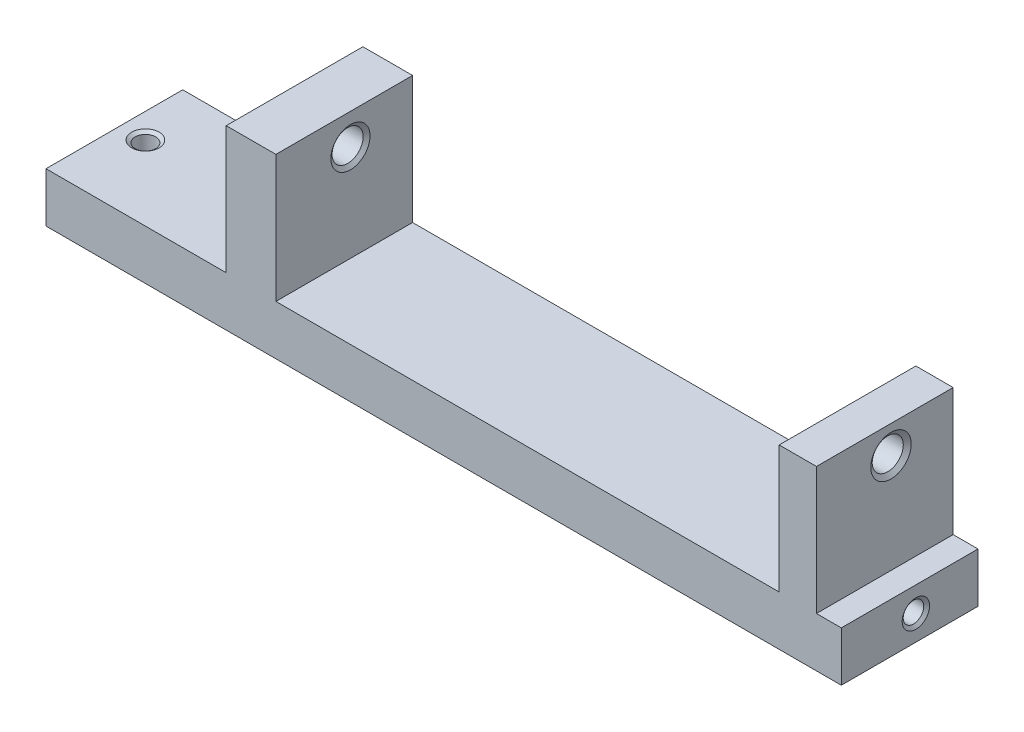
SolidWorks part; units mm, degrees
ref_plane "Спереди" through (0, 0, 0) normal (0, 0, 1) x (1, 0, 0)
ref_plane "Сверху" through (0, 0, 0) normal (0, 1, 0) x (1, 0, 0)
ref_plane "Справа" through (0, 0, 0) normal (1, 0, 0) x (0, 0, -1)
sketch "Эскиз1" plane through (0, 0, 0) normal (0, 0, 1) x (1, 0, 0)
  line L0 (0, 0) -> (128, 0)
  line L1 (128, 0) -> (128, 8)
  line L2 (124, 28.5) -> (118, 28.5)
  line L3 (118, 28.5) -> (118, 8)
  line L4 (118, 8) -> (37, 8)
  line L5 (37, 8) -> (37, 28.5)
  line L6 (37, 28.5) -> (29, 28.5)
  line L7 (29, 28.5) -> (29, 8)
  line L8 (29, 8) -> (0, 8)
  line L9 (0, 8) -> (0, 0)
  line L10 (128, 8) -> (124, 8)
  line L11 (124, 8) -> (124, 28.5)
  dimension "D1" = 128
  dimension "D2" = 8
  dimension "D3" = 6
  dimension "D4" = 8
  dimension "D5" = 81
  dimension "D6" = 4
  dimension "D7" = 28.5
extrude "Бобышка-Вытянуть1" add sketch "Эскиз1" along normal blind 22
hole_wizard "Отверстие обработанное метчиком M6x1.01" positions "Эскиз3" profile "Эскиз2" tap size "M6x1.0" standard "Ansi (метрические)" end condition up to next
sketch "Эскиз3" plane through (29, 0, 0) normal (-1, 0, 0) x (0, 0, 1)
  line L1 (22, 0) -> (0, 0) construction
  line L2 (0, 28.5) -> (0, 8) construction
  point P0 (10, 23.5)
  dimension "D1" = 10
  dimension "D2" = 23.5
sketch "Эскиз2" plane through (29, 23.5, 10) normal (0, 1, 0) x (0, 0, 1)
  line L0 (0, 0) -> (0, 8)
  line L1 (0, 8) -> (3.15, 8)
  line L2 (2.5, 7.5449) -> (2.5, 0.4551)
  line L3 (2.5, 0.4551) -> (3.15, 0)
  line L5 (3.15, 0) -> (0, 0)
  line L6 (-2.5, 0.4551) -> (-3.15, 0) construction
  line L7 (3.15, 8) -> (2.5, 7.5449)
  line L8 (-3.15, 8) -> (-2.5, 7.5449) construction
  line L11 (0, -6.35) -> (0, 107.95) construction
  dimension "Диаметр резьбы" = 5
  dimension "Глубина проходного сверла" = 8
  dimension "Диаметр передней зенковки" = 6.3
  dimension "Угол передней зенковки" = 110
  dimension "Диаметр задней зенковки" = 6.3
  dimension "Угол задней зенковки" = 110
hole_wizard "Отверстие обработанное метчиком M6x1.02" positions "Эскиз5" profile "Эскиз4" tap size "M6x1.0" standard "Ansi (метрические)" end condition up to next
sketch "Эскиз5" plane through (124, -10.4422, 3.3226) normal (1, 0, 0) x (0, 0, -1)
  line L1 (-18.6774, 10.4422) -> (3.3226, 10.4422) construction
  line L2 (3.3226, 18.4422) -> (3.3226, 38.9422) construction
  point P0 (-6.6774, 34.4422)
  dimension "D1" = 10
  dimension "D2" = 24
sketch "Эскиз4" plane through (124, 24, 10) normal (0, 1, 0) x (0, 0, -1)
  line L0 (0, 0) -> (0, 6)
  line L1 (0, 6) -> (3.25, 6)
  line L2 (2.5, 5.4748) -> (2.5, 0.5252)
  line L3 (2.5, 0.5252) -> (3.25, 0)
  line L5 (3.25, 0) -> (0, 0)
  line L6 (-2.5, 0.5252) -> (-3.25, 0) construction
  line L7 (3.25, 6) -> (2.5, 5.4748)
  line L8 (-3.25, 6) -> (-2.5, 5.4748) construction
  line L11 (0, -6.35) -> (0, 107.95) construction
  dimension "Диаметр резьбы" = 5
  dimension "Глубина проходного сверла" = 6
  dimension "Диаметр передней зенковки" = 6.5
  dimension "Угол передней зенковки" = 110
  dimension "Диаметр задней зенковки" = 6.5
  dimension "Угол задней зенковки" = 110
hole_wizard "Отверстие обработанное метчиком M4x0.71" positions "Эскиз7" profile "Эскиз6" tap size "M4x0.7" standard "Ansi (метрические)" end condition up to next
sketch "Эскиз7" plane through (0, 0, 0) normal (0, -1, 0) x (1, 0, 0)
  line L0 (0, 0) -> (128, 0) construction
  line L1 (0, 22) -> (0, 0) construction
  point P0 (4, 10)
  dimension "D1" = 10
  dimension "D2" = 4
sketch "Эскиз6" plane through (4, 0, 10) normal (1, 0, 0) x (0, 0, -1)
  line L0 (0, 0) -> (0, 8)
  line L1 (0, 8) -> (2.2, 8)
  line L2 (1.65, 7.6149) -> (1.65, 0.3851)
  line L3 (1.65, 0.3851) -> (2.2, 0)
  line L5 (2.2, 0) -> (0, 0)
  line L6 (-1.65, 0.3851) -> (-2.2, 0) construction
  line L7 (2.2, 8) -> (1.65, 7.6149)
  line L8 (-2.2, 8) -> (-1.65, 7.6149) construction
  line L11 (0, -6.35) -> (0, 107.95) construction
  dimension "Диаметр резьбы" = 3.3
  dimension "Глубина проходного сверла" = 8
  dimension "Диаметр передней зенковки" = 4.4
  dimension "Угол передней зенковки" = 110
  dimension "Диаметр задней зенковки" = 4.4
  dimension "Угол задней зенковки" = 110
hole_wizard "Отверстие обработанное метчиком M4x0.72" positions "Эскиз9" profile "Эскиз8" tap size "M4x0.7" standard "Ansi (метрические)"
sketch "Эскиз9" plane through (128, 0, 0) normal (1, 0, 0) x (0, 0, -1)
  line L0 (-22, 0) -> (0, 0) construction
  line L1 (0, 0) -> (0, 8) construction
  point P0 (-10, 4)
  dimension "D1" = 4
  dimension "D2" = 10
sketch "Эскиз8" plane through (128, 4, 10) normal (0, 1, 0) x (0, 0, -1)
  line L0 (0, 0) -> (0, 12.4914)
  line L1 (0, 12.4914) -> (1.65, 11.5)
  line L2 (1.65, 11.5) -> (1.65, 0.3851)
  line L3 (1.65, 0.3851) -> (2.2, 0)
  line L5 (2.2, 0) -> (0, 0)
  line L6 (-1.65, 0.3851) -> (-2.2, 0) construction
  line L10 (0, 12.4914) -> (-1.65, 11.5) construction
  line L11 (0, -6.35) -> (0, 107.95) construction
  dimension "Диаметр сверла" = 3.3
  dimension "Глубина сверла" = 11.5
  dimension "Диаметр передней зенковки" = 4.4
  dimension "Угол передней зенковки" = 110
  dimension "Угол заточки сверла" = 118
